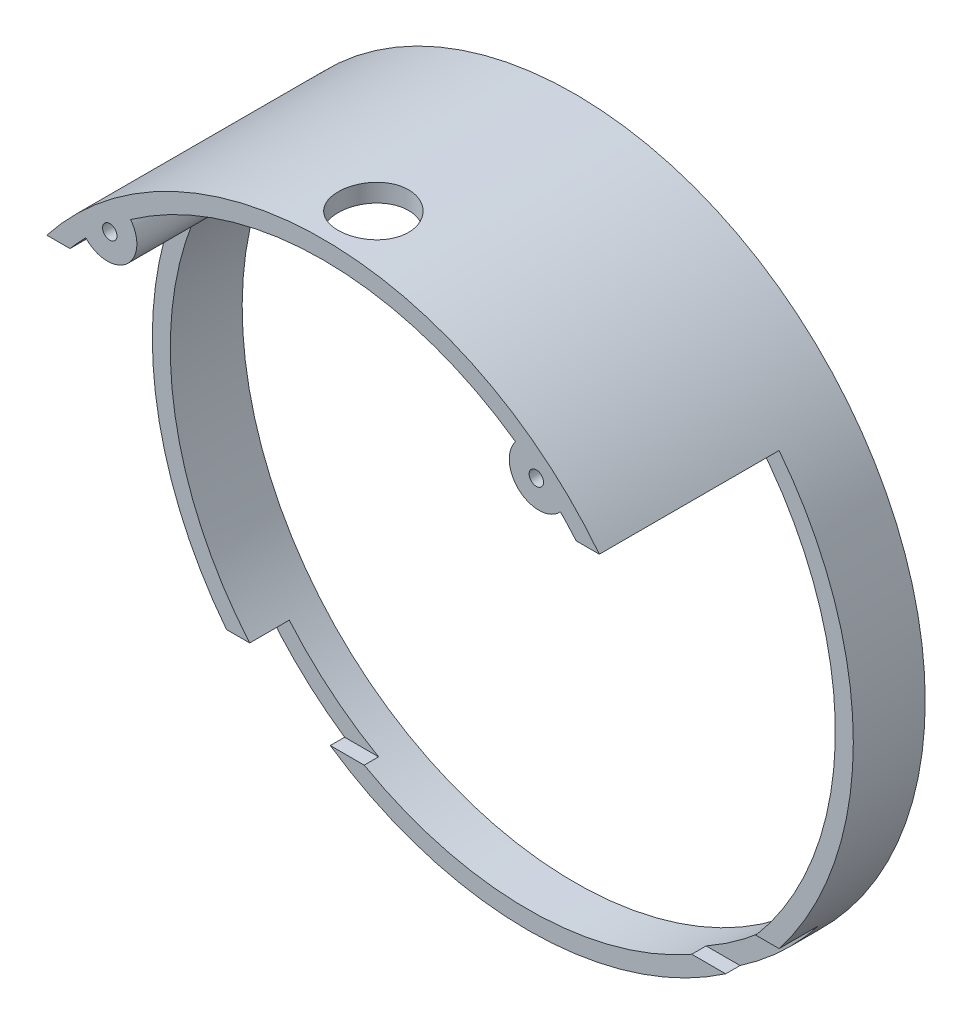
SolidWorks part; units mm, degrees
ref_plane "Front Plane" through (0, 0, 0) normal (0, 0, 1) x (1, 0, 0)
ref_plane "Top Plane" through (0, 0, 0) normal (0, 1, 0) x (1, 0, 0)
ref_plane "Right Plane" through (0, 0, 0) normal (1, 0, 0) x (0, 0, -1)
sketch "Sketch2" plane through (0, 0, 0) normal (0, 0, 1) x (1, 0, 0)
  circle A0 centre (0, 0) radius 97.5
  circle A1 centre (0, 0) radius 92.5
  dimension "D1" = 185
  dimension "D2" = 195
extrude "Boss-Extrude1" add sketch "Sketch2" along normal blind 70
sketch "Sketch3" plane through (0, 0, 0) normal (0, 1, 0) x (1, 0, 0)
  line L0 (-97.5, -70) -> (97.5, -70) construction
  line L1 (-55, -127) -> (55, -127)
  line L2 (-55, -127) -> (-55, -13)
  line L3 (-55, -13) -> (55, -13)
  line L4 (55, -127) -> (55, -13)
  line L5 (-55, -127) -> (55, -13) construction
  line L6 (-55, -13) -> (55, -127) construction
  line L7 (92.5, 0) -> (-92.5, 0) construction
  point P0 (0, -70)
  dimension "D1" = 13
  dimension "D2" = 110
extrude "Cut-Extrude1" cut sketch "Sketch3" against normal through all
sketch "Sketch4" plane through (0, 0, 0) normal (1, 0, 0) x (0, 0, -1)
  line L0 (-70, 97.5) -> (-70, -80.5062) construction
  line L1 (-120, 60) -> (-20, 60)
  line L2 (-120, 60) -> (-120, -60)
  line L3 (-120, -60) -> (-20, -60)
  line L4 (-20, 60) -> (-20, -60)
  line L5 (-120, 60) -> (-20, -60) construction
  line L6 (-120, -60) -> (-20, 60) construction
  line L7 (0, -97.5) -> (0, 97.5) construction
  point P0 (-70, 0)
  dimension "D1" = 120
  dimension "D2" = 20
extrude "Cut-Extrude2" cut sketch "Sketch4" against normal through all both and the other way through all
sketch "Sketch5" plane through (0, 0, 0) normal (1, 0, 0) x (0, 0, -1)
  line L0 (0, -97.5) -> (0, 97.5) construction
  line L1 (-70, -80.5062) -> (-9, -80.5062)
  line L2 (-70, -80.5062) -> (-70, -60)
  line L3 (-70, -60) -> (-9, -60)
  line L4 (-9, -80.5062) -> (-9, -60)
  dimension "D1" = 9
extrude "Cut-Extrude3" cut sketch "Sketch5" against normal through all both and the other way through all
sketch "Sketch6" plane through (0, 0, 0) normal (0, 1, 0) x (1, 0, 0)
  circle A0 centre (0, -56.0129) radius 9.7843
extrude "Cut-Extrude4" cut sketch "Sketch6" along normal through all
sketch "Sketch8" plane through (0, 0, 0) normal (0, 0, 1) x (1, 0, 0)
  arc A0 (66.021, 64.7879) -> (53.5302, 75.4372) centre (60.0123, 70.3902) cw
  circle A1 centre (0, 0) radius 92.5 construction
  arc A2 (53.5302, 75.4372) -> (66.021, 64.7879) centre (0, 0) cw
extrude "Boss-Extrude2" add sketch "Sketch8" along normal blind 70
sketch "Sketch9" plane through (0, 0, 0) normal (0, 0, -1) x (-1, 0, 0)
  circle A0 centre (-59.3269, 69.5719) radius 2
  point P3 (-59.3269, 69.5719)
  dimension "D1" = 4
extrude "Cut-Extrude5" cut sketch "Sketch9" against normal through all
mirror "Mirror1" about plane through (0, 0, 0) normal (1, 0, 0) of "Cut-Extrude5", "Boss-Extrude2"
